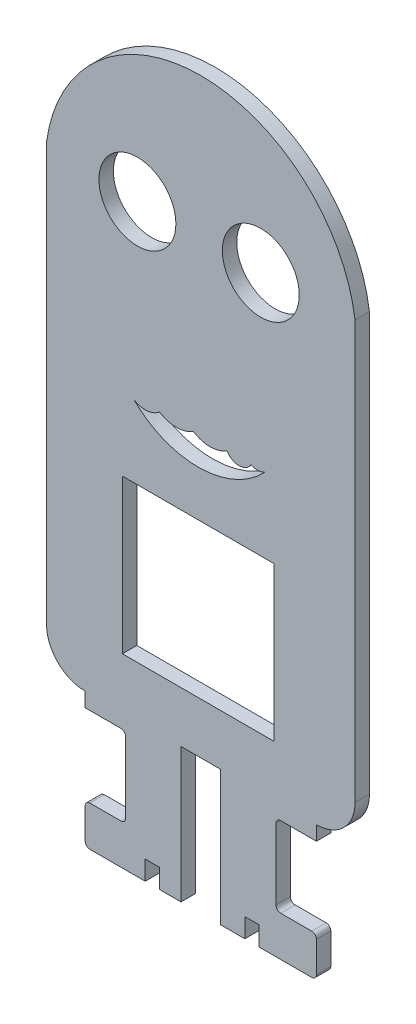
SolidWorks part; units mm, degrees
ref_plane "Alzado" through (0, 0, 0) normal (0, 0, 1) x (1, 0, 0)
ref_plane "Planta" through (0, 0, 0) normal (0, 1, 0) x (1, 0, 0)
ref_plane "Vista lateral" through (0, 0, 0) normal (1, 0, 0) x (0, 0, -1)
sketch "Model" plane through (0, 0, 0) normal (0, 0, 1) x (1, 0, 0)
  line L0 (8.3054, 8.1464) -> (-6.9812, 8.1464)
  line L1 (8.3054, -23.8536) -> (8.3054, 8.1464)
  line L2 (-23.2679, -23.8536) -> (8.3054, -23.8536)
  line L3 (-23.2679, 8.1464) -> (-23.2679, -23.8536)
  line L4 (-6.9812, 8.1464) -> (-23.2679, 8.1464)
  line L5 (25.1034, 60.4498) -> (25.1034, 55.56)
  line L6 (9.6448, -54.107) -> (16.0907, -54.107)
  line L7 (8.6581, -38.4391) -> (8.6581, -53.107)
  line L8 (17.0773, -37.4392) -> (9.6346, -37.4392)
  line L9 (17.0773, -36.4392) -> (17.0773, -37.4392)
  line L10 (-18.5256, -62.44) -> (-30.0173, -62.44)
  line L11 (-18.5256, -58.44) -> (-18.5256, -62.44)
  line L12 (-15.5656, -58.44) -> (-18.5256, -58.44)
  line L13 (-15.5656, -62.44) -> (-15.5656, -58.44)
  line L14 (-11.0742, -62.44) -> (-15.5656, -62.44)
  line L15 (-11.0742, -34.44) -> (-11.0742, -62.44)
  line L16 (-2.8524, -34.44) -> (-11.0742, -34.44)
  line L17 (-2.8524, -62.44) -> (-2.8524, -34.44)
  line L18 (2.1944, -62.44) -> (-2.8524, -62.44)
  line L19 (2.1944, -58.44) -> (2.1944, -62.44)
  line L20 (5.1544, -58.44) -> (2.1944, -58.44)
  line L21 (5.1544, -62.44) -> (5.1544, -58.44)
  line L22 (16.0907, -62.44) -> (5.1544, -62.44)
  line L23 (17.0773, -61.44) -> (17.0773, -55.107)
  line L24 (25.1034, 55.56) -> (25.1034, -26.4392)
  line L25 (-31.0039, -61.44) -> (-31.0039, -55.107)
  line L26 (-39.03, -26.44) -> (-39.03, 60.4498)
  line L27 (17.0773, -34.4392) -> (17.0773, -36.4392)
  line L28 (17.21, -34.4392) -> (17.0773, -34.4392)
  line L29 (-31.0039, -34.44) -> (-31.1366, -34.44)
  line L30 (-31.0039, -37.44) -> (-31.0039, -34.44)
  line L31 (-23.5714, -37.44) -> (-31.0039, -37.44)
  line L32 (-22.5847, -53.107) -> (-22.5847, -38.44)
  line L33 (-30.0173, -54.107) -> (-23.5714, -54.107)
  arc A0 (17.0773, -55.107) -> (16.0907, -54.107) centre (16.084, -55.1003) ccw
  arc A1 (8.6581, -53.107) -> (9.6448, -54.107) centre (9.6514, -53.1136) ccw
  arc A2 (9.6346, -37.4392) -> (8.6581, -38.4391) centre (9.6515, -38.4324) ccw
  arc A3 (16.0907, -62.44) -> (17.0773, -61.44) centre (16.084, -61.4466) ccw
  arc A4 (-31.0039, -61.44) -> (-30.0173, -62.44) centre (-30.0106, -61.4466) ccw
  arc A5 (25.1034, 60.4498) -> (22.3614, 69.755) centre (-6.9633, 56.0575) ccw
  arc A6 (3.47, 23.56) -> (6.5243, 23.8231) centre (4.782, 26.1902) ccw
  arc A7 (-1.53, 23.56) -> (3.47, 23.56) centre (0.97, 25.06) ccw
  arc A8 (-8.53, 23.56) -> (-1.53, 23.56) centre (-5.03, 29.06) ccw
  arc A9 (-15.53, 23.56) -> (-8.53, 23.56) centre (-12.03, 29.06) ccw
  arc A10 (-20.963, 23.1881) -> (-15.53, 23.56) centre (-18.4942, 26.9934) ccw
  arc A11 (-20.963, 23.1881) -> (6.5243, 23.8231) centre (-7.5235, 36.6745) ccw
  arc A12 (22.3614, 69.755) -> (-39.03, 60.4498) centre (-6.9633, 56.0575) ccw
  arc A13 (17.21, -34.4392) -> (25.1034, -26.4392) centre (17.1567, -26.4925) ccw
  arc A14 (-39.03, -26.44) -> (-31.1366, -34.44) centre (-31.0833, -26.4933) ccw
  arc A15 (-22.5847, -38.44) -> (-23.5714, -37.44) centre (-23.578, -38.4333) ccw
  arc A16 (-23.5714, -54.107) -> (-22.5847, -53.107) centre (-23.578, -53.1136) ccw
  arc A17 (-30.0173, -54.107) -> (-31.0039, -55.107) centre (-30.0106, -55.1003) ccw
  circle A18 centre (5.5107, 59.1356) radius 8
  circle A19 centre (-20.1427, 59.1356) radius 8
extrude "Saliente-Extruir1" add sketch "Model" along normal blind 3
